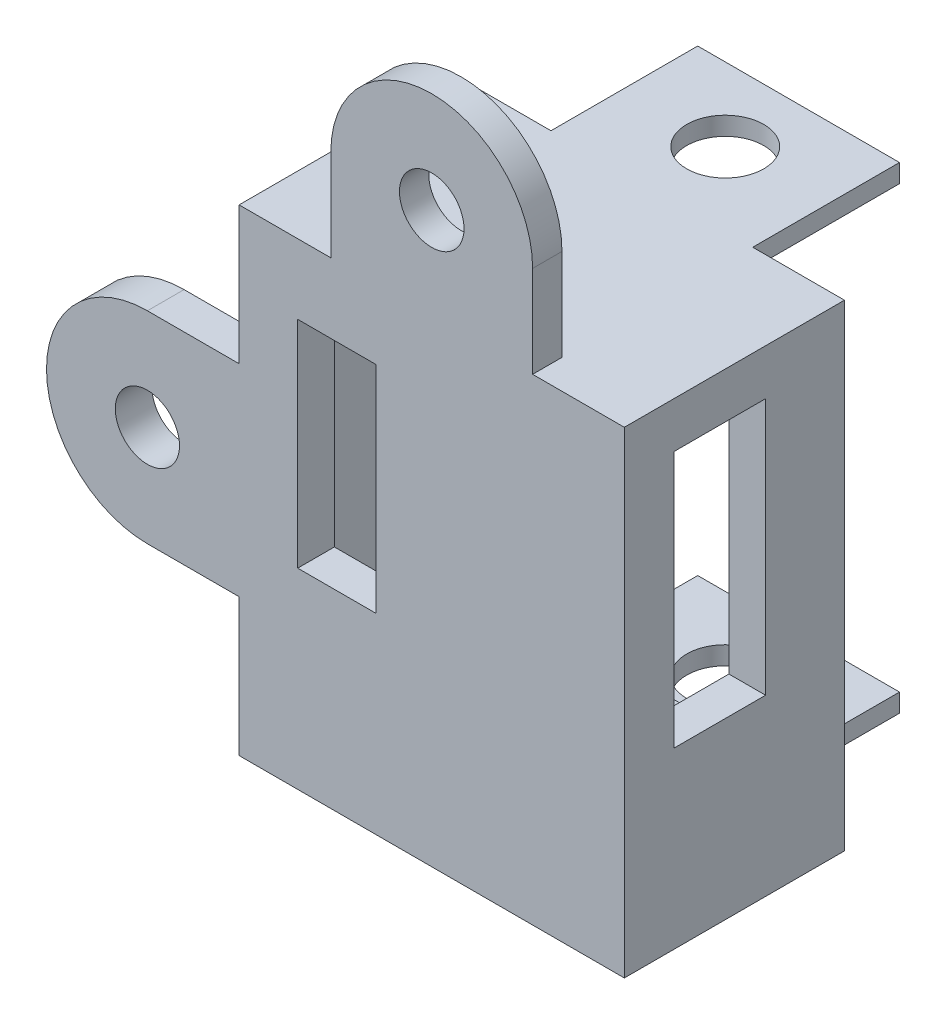
SolidWorks part; units mm, degrees
material "ABS PC"
ref_plane "Front Plane" through (0, 0, 0) normal (0, 0, 1) x (1, 0, 0)
ref_plane "Top Plane" through (0, 0, 0) normal (0, 1, 0) x (1, 0, 0)
ref_plane "Right Plane" through (0, 0, 0) normal (1, 0, 0) x (0, 0, -1)
sketch "Sketch1" plane through (0, 0, 0) normal (0, 0, 1) x (1, 0, 0)
  line L1 (-8.5, -10.5) -> (8.5, -10.5)
  line L2 (-8.5, -10.5) -> (-8.5, 10.5)
  line L3 (-8.5, 10.5) -> (8.5, 10.5)
  line L4 (8.5, -10.5) -> (8.5, 10.5)
  line L5 (-8.5, -10.5) -> (8.5, 10.5) construction
  line L6 (-8.5, 10.5) -> (8.5, -10.5) construction
  line L7 (-10.5, -13) -> (10.5, -13)
  line L8 (-10.5, -13) -> (-10.5, 13)
  line L9 (-10.5, 13) -> (10.5, 13)
  line L10 (10.5, -13) -> (10.5, 13)
  line L11 (-10.5, -13) -> (10.5, 13) construction
  line L12 (-10.5, 13) -> (10.5, -13) construction
  point P0 (0, 0)
  point P5 (0, 0)
  dimension "D1" = 21
  dimension "D2" = 17
  dimension "D3" = 21
  dimension "D4" = 26
extrude "Boss-Extrude1" add sketch "Sketch1" along normal blind 10
sketch "Sketch2" plane through (0, 0, 10) normal (0, 0, 1) x (1, 0, 0)
  line L1 (-10.5, -13) -> (10.5, -13)
  line L2 (-10.5, -13) -> (-10.5, 13)
  line L3 (-10.5, 13) -> (10.5, 13)
  line L4 (10.5, -13) -> (10.5, 13)
  line L5 (-10.5, -13) -> (10.5, 13) construction
  line L6 (-10.5, 13) -> (10.5, -13) construction
  point P0 (0, 0)
  dimension "D1" = 26
  dimension "D2" = 21
extrude "Boss-Extrude2" add sketch "Sketch2" along normal blind 2
sketch "Sketch4" plane through (10.5, 0, 0) normal (1, 0, 0) x (0, 0, -1)
  line L0 (0, 13) -> (-4.3, 13)
  line L1 (-12, 13) -> (0, 13) construction
  line L2 (-4.3, 13) -> (-4.3, 10.5)
  line L3 (-4.3, 10.5) -> (-4.3, -3.5)
  line L4 (-4.3, -3.5) -> (-9.3, -3.5)
  line L7 (-9.3, -3.5) -> (-9.3, 10.5)
  line L8 (-9.3, 10.5) -> (-4.3, 10.5)
  dimension "D1" = 4.3
  dimension "D2" = 2.5
  dimension "D3" = 14
  dimension "D4" = 5
extrude "Cut-Extrude2" cut sketch "Sketch4" against normal blind 2 contours L8 L7 L4 L3
sketch "Sketch6" plane through (0, 0, 12) normal (0, 0, 1) x (1, 0, 0)
  line L0 (0, 13) -> (5.5, 13)
  line L1 (10.5, 13) -> (-10.5, 13) construction
  line L2 (0, 13) -> (-5.5, 13)
  line L3 (-5.5, 13) -> (-5.5, 18)
  line L4 (5.5, 13) -> (5.5, 18)
  arc A0 (5.5, 18) -> (-5.5, 18) centre (0, 18) ccw
  circle A1 centre (0, 18) radius 1.76
  dimension "D4" = 3.52
  dimension "D1" = 5.5
  dimension "D2" = 5.5
  dimension "D3" = 5
extrude "Boss-Extrude3" add sketch "Sketch6" against normal blind 1.6
sketch "Sketch9" plane through (0, 0, 12) normal (0, 0, 1) x (1, 0, 0)
  line L0 (0, -13) -> (-5.5, -13)
  line L1 (-10.5, -13) -> (10.5, -13) construction
  line L2 (0, -13) -> (5.5, -13)
  line L3 (5.5, -13) -> (5.5, -18)
  line L4 (-5.5, -13) -> (-5.5, -18)
  arc A0 (-5.5, -18) -> (5.5, -18) centre (0, -18) ccw
  circle A1 centre (0, -18) radius 1.76
  dimension "D5" = 3.52
  dimension "D1" = 5.5
  dimension "D2" = 5.5
  dimension "D3" = 5
  dimension "D4" = 5
extrude "Boss-Extrude5" add sketch "Sketch9" against normal blind 2
sketch "Sketch14" plane through (0, 0, 0) normal (0, 0, -1) x (-1, 0, 0)
  line L0 (-5.5, -13) -> (5.5, -13)
  line L1 (5.5, -13) -> (5.5, -12)
  line L2 (5.5, -12) -> (-5.5, -12)
  line L3 (-5.5, -12) -> (-5.5, -13)
  line L4 (-5.5, 13) -> (5.5, 13)
  line L5 (5.5, 13) -> (5.5, 12)
  line L6 (5.5, 12) -> (-5.5, 12)
  line L7 (-5.5, 12) -> (-5.5, 13)
  dimension "D1" = 1
  dimension "D2" = 1
extrude "Boss-Extrude8" add sketch "Sketch14" along normal blind 8
sketch "Sketch16" plane through (0, 13, 0) normal (0, 1, 0) x (1, 0, 0)
  line L0 (0, 0) -> (0, 4)
  circle A0 centre (0, 4) radius 2.1
  dimension "D2" = 4.2
  dimension "D1" = 4
extrude "Cut-Extrude3" cut sketch "Sketch16" against normal blind 39
sketch "Sketch17" plane through (0, 0, 10) normal (0, 0, -1) x (-1, 0, 0)
  line L0 (-5.5, -18) -> (-5.5, -13)
  line L1 (-5.5, -13) -> (5.5, -13)
  line L2 (5.5, -13) -> (5.5, -18)
  arc A0 (5.5, -18) -> (-5.5, -18) centre (0, -18) cw
extrude "Cut-Extrude4" cut sketch "Sketch17" against normal blind 10
sketch "Sketch18" plane through (0, 0, 12) normal (0, 0, 1) x (1, 0, 0)
  line L0 (-10.5, 0) -> (-10.5, 5.5)
  line L1 (-10.5, 13) -> (-10.5, -13) construction
  line L2 (-10.5, 5.5) -> (-15.5, 5.5)
  line L3 (-10.5, 0) -> (-10.5, -5.5)
  line L4 (-10.5, -5.5) -> (-15.5, -5.5)
  arc A0 (-15.5, -5.5) -> (-15.5, 5.5) centre (-15.5, 0) cw
  circle A1 centre (-15.5, 0) radius 1.75
  dimension "D4" = 3.5
  dimension "D1" = 5
  dimension "D2" = 5.5
  dimension "D3" = 5.5
extrude "Boss-Extrude9" add sketch "Sketch18" against normal blind 2
sketch "Sketch19" plane through (0, 0, 10) normal (0, 0, -1) x (-1, 0, 0)
  line L1 (7.3059, 9.194) -> (3.0257, 9.194)
  line L2 (7.3059, 9.194) -> (7.3059, -2.5539)
  line L3 (7.3059, -2.5539) -> (3.0257, -2.5539)
  line L4 (3.0257, 9.194) -> (3.0257, -2.5539)
extrude "Cut-Extrude5" cut sketch "Sketch19" against normal blind 10
